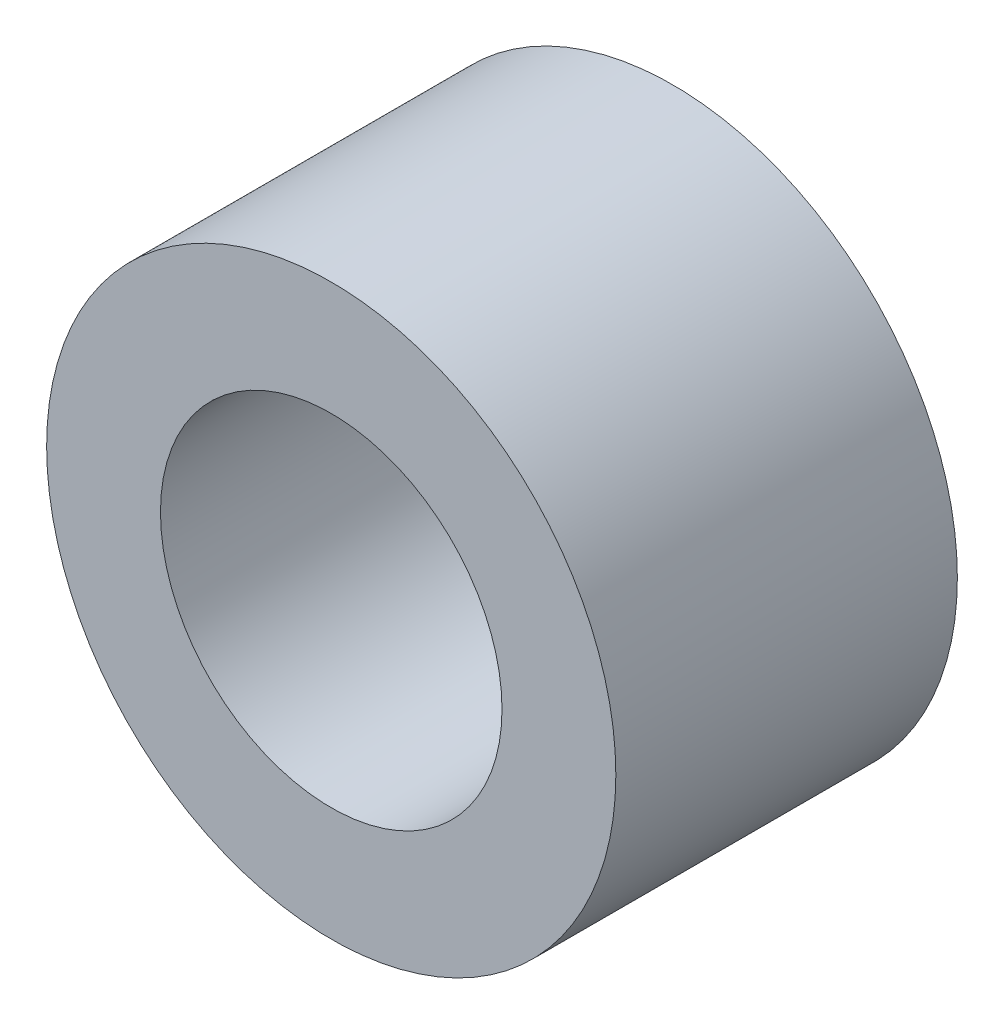
SolidWorks part; units mm, degrees
ref_plane "Front Plane" through (0, 0, 0) normal (0, 0, 1) x (1, 0, 0)
ref_plane "Top Plane" through (0, 0, 0) normal (0, 1, 0) x (1, 0, 0)
ref_plane "Right Plane" through (0, 0, 0) normal (1, 0, 0) x (0, 0, -1)
sketch "Sketch1" plane through (0, 0, 0) normal (0, 0, 1) x (1, 0, 0)
  circle A0 centre (0, 0) radius 31.75
  dimension "D1" = 63.5
extrude "Boss-Extrude1" add sketch "Sketch1" along normal blind 38.1
sketch "Sketch2" plane through (0, 0, 0) normal (0, 0, -1) x (-1, 0, 0)
  circle A0 centre (0, 0) radius 19.05
  dimension "D1" = 38.1
extrude "Cut-Extrude1" cut sketch "Sketch2" against normal blind 12.7
sketch "Sketch3" plane through (0, 0, 38.1) normal (0, 0, 1) x (1, 0, 0)
  circle A0 centre (0, 0) radius 19.05
  dimension "D1" = 38.1
extrude "Cut-Extrude2" cut sketch "Sketch3" against normal through all
sketch "Sketch4" plane through (0, 0, 0) normal (0, 0, -1) x (-1, 0, 0)
  circle A0 centre (0, 0) radius 22.86
  dimension "D1" = 45.72
extrude "Cut-Extrude3" cut sketch "Sketch4" against normal blind 7.62
